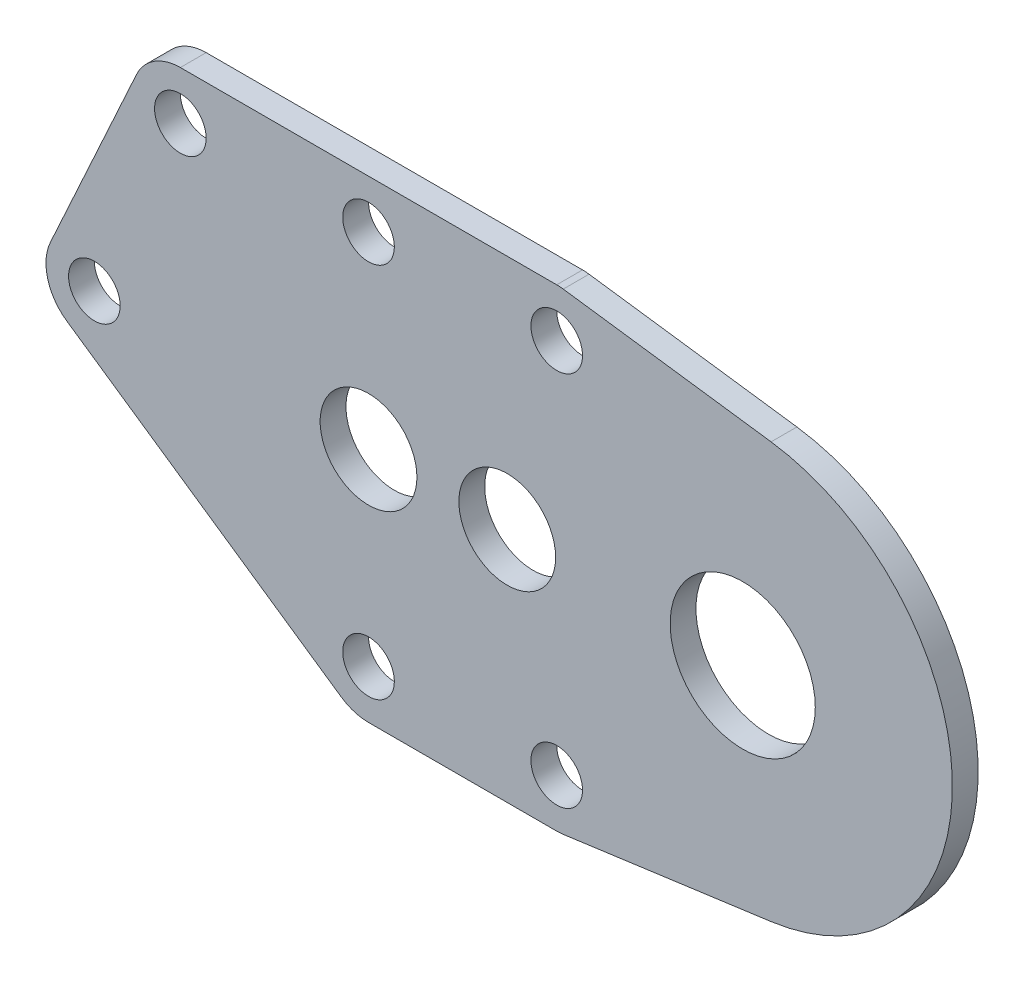
SolidWorks part; units mm, degrees
ref_plane "Front" through (0, 0, 0) normal (0, 0, 1) x (1, 0, 0)
ref_plane "Top" through (0, 0, 0) normal (0, 1, 0) x (1, 0, 0)
ref_plane "Right" through (0, 0, 0) normal (1, 0, 0) x (0, 0, -1)
sketch "Sketch1" plane through (0, 0, 0) normal (0, 0, 1) x (1, 0, 0)
  line L9 (12.0731, 14.6397) -> (24.9585, 12.8805)
  line L15 (12.0731, -14.6397) -> (24.9585, -12.8805)
  line L16 (11.6673, 14.6673) -> (-11.6673, 14.6673)
  line L17 (11.6673, -14.6673) -> (0, -14.6673)
  line L18 (-14.3958, 12.9144) -> (-19.7285, 1.2471)
  line L19 (-18.6976, -2.4735) -> (-1.6976, -14.1408)
  circle A17 centre (0, 0) radius 3
  circle A18 centre (23.2, 0) radius 4.5
  circle A19 centre (8.6, 0) radius 3
  circle A24 centre (-17, 0) radius 1.6
  arc A26 (12.0731, 14.6397) -> (11.6673, 14.6673) centre (11.6673, 11.6673) ccw
  arc A28 (-11.6673, 14.6673) -> (-14.3958, 12.9144) centre (-11.6673, 11.6673) ccw
  arc A29 (11.6673, -14.6673) -> (12.0731, -14.6397) centre (11.6673, -11.6673) ccw
  arc A30 (-1.6976, -14.1408) -> (0, -14.6673) centre (0, -11.6673) ccw
  arc A31 (-19.7285, 1.2471) -> (-18.6976, -2.4735) centre (-17, 0) ccw
  circle A32 centre (0, -11.6673) radius 1.6
  circle A33 centre (11.6673, -11.6673) radius 1.6
  circle A34 centre (-11.6673, 11.6673) radius 1.6
  circle A35 centre (0, 11.6673) radius 1.6
  circle A36 centre (11.6673, 11.6673) radius 1.6
  arc A37 (24.9585, -12.8805) -> (24.9585, 12.8805) centre (23.2, 0) ccw
extrude "Boss-Extrude3" add sketch "Sketch1" along normal blind 1.6
